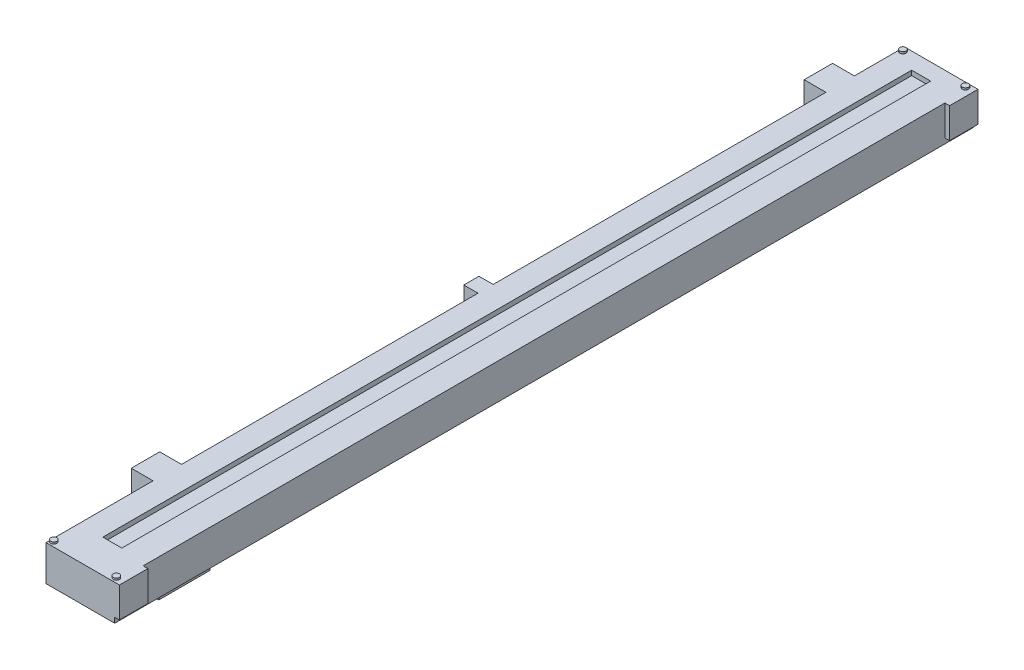
SolidWorks part; units mm, degrees
material "Delrin 2700 NC010, Low Viscosity Acetal Copolymer (SS)"
ref_plane "Front Plane" through (0, 0, 0) normal (0, 0, 1) x (1, 0, 0)
ref_plane "Top Plane" through (0, 0, 0) normal (0, 1, 0) x (1, 0, 0)
ref_plane "Right Plane" through (0, 0, 0) normal (1, 0, 0) x (0, 0, -1)
sketch "Sketch1" plane through (0, 0, 0) normal (0, 1, 0) x (1, 0, 0)
  line L0 (-9.2075, 115.0938) -> (9.2075, -115.0938) construction
  line L1 (-9.2075, 115.0938) -> (9.2075, 115.0938)
  line L2 (-9.2075, 115.0938) -> (-9.2075, -115.0938)
  line L3 (-9.2075, -115.0938) -> (9.2075, -115.0938)
  line L4 (9.2075, 115.0938) -> (9.2075, -115.0938)
  dimension "D1" = 18.415
  dimension "D2" = 230.1875
extrude "Boss-Extrude1" add sketch "Sketch1" along normal blind 9.525
sketch "Sketch2" plane through (0, 9.525, 0) normal (0, 1, 0) x (1, 0, 0)
  line L0 (-2.8575, 110.6487) -> (2.2225, -106.2038) construction
  line L1 (-2.8575, 110.6487) -> (2.2225, 110.6487)
  line L2 (-2.8575, 110.6487) -> (-2.8575, -106.2038)
  line L3 (-2.8575, -106.2038) -> (2.2225, -106.2038)
  line L4 (2.2225, 110.6487) -> (2.2225, -106.2038)
  line L5 (9.2075, 115.0938) -> (-9.2075, 115.0938) construction
  line L6 (-9.2075, -115.0938) -> (9.2075, -115.0938) construction
  line L8 (-9.2075, 115.0938) -> (-9.2075, -115.0938) construction
  dimension "D1" = 5.08
  dimension "D2" = 4.445
  dimension "D3" = 8.89
  dimension "D4" = 6.35
extrude "Cut-Extrude1" cut sketch "Sketch2" against normal blind 1.27
sketch "Sketch3" plane through (0, 9.525, 0) normal (0, 1, 0) x (1, 0, 0)
  line L0 (-9.2075, 115.0938) -> (-9.2075, -115.0938) construction
  line L1 (-9.2075, 101.6317) -> (-15.0495, 101.6317)
  line L2 (-9.2075, 101.6317) -> (-9.2075, 94.0117)
  line L3 (-9.2075, 94.0117) -> (-15.0495, 94.0117)
  line L4 (-15.0495, 101.6317) -> (-15.0495, 94.0117)
  line L5 (-9.2075, -115.0938) -> (9.2075, -115.0938) construction
  line L6 (-9.2075, 4.7942) -> (-13.0175, 4.7942)
  line L7 (-9.2075, 4.7942) -> (-9.2075, 0.7302)
  line L8 (-9.2075, 0.7302) -> (-13.0175, 0.7302)
  line L9 (-13.0175, 4.7942) -> (-13.0175, 0.7302)
  line L10 (-9.2075, -78.7718) -> (-15.0495, -78.7718)
  line L11 (-9.2075, -78.7718) -> (-9.2075, -86.3918)
  line L12 (-9.2075, -86.3918) -> (-15.0495, -86.3918)
  line L13 (-15.0495, -78.7718) -> (-15.0495, -86.3918)
  line L14 (9.2075, 115.0938) -> (-9.2075, 115.0938) construction
  line L15 (9.2075, -115.0938) -> (9.2075, 115.0938) construction
  line L16 (9.2075, 115.0938) -> (10.4775, 115.0938)
  line L17 (9.2075, 115.0938) -> (9.2075, 107.4737)
  line L18 (9.2075, 107.4737) -> (10.4775, 107.4737)
  line L19 (10.4775, 115.0938) -> (10.4775, 107.4737)
  line L20 (9.2075, -115.0938) -> (10.4775, -115.0938)
  line L21 (9.2075, -115.0938) -> (9.2075, -107.4738)
  line L22 (9.2075, -107.4738) -> (10.4775, -107.4738)
  line L23 (10.4775, -115.0938) -> (10.4775, -107.4738)
  dimension "D1" = 7.62
  dimension "D2" = 5.842
  dimension "D3" = 28.702
  dimension "D4" = 13.462
  dimension "D5" = 115.824
  dimension "D6" = 4.064
  dimension "D7" = 3.81
  dimension "D8" = 7.62
  dimension "D9" = 1.27
extrude "Boss-Extrude2" add sketch "Sketch3" against normal blind 8.128
sketch "Sketch4" plane through (0, 9.525, 0) normal (0, 1, 0) x (1, 0, 0)
  line L1 (8.382, 113.8237) -> (-8.382, 113.8238) construction
  line L2 (8.382, 113.8237) -> (8.382, -113.8238) construction
  line L3 (8.382, -113.8238) -> (-8.382, -113.8238) construction
  line L4 (-8.382, 113.8238) -> (-8.382, -113.8238) construction
  line L6 (9.2075, -107.4738) -> (9.2075, 107.4737) construction
  line L7 (-9.2075, 115.0938) -> (-9.2075, 101.6317) construction
  line L8 (10.4775, 115.0938) -> (-9.2075, 115.0938) construction
  line L9 (-9.2075, -115.0938) -> (10.4775, -115.0938) construction
  circle A0 centre (-8.382, 113.8238) radius 0.8255
  circle A1 centre (8.382, 113.8237) radius 0.8255
  circle A2 centre (8.382, -113.8238) radius 0.8255
  circle A3 centre (-8.382, -113.8238) radius 0.8255
  dimension "D1" = 1.651
  dimension "D2" = 1.27
  dimension "D3" = 1.27
extrude "Boss-Extrude3" add sketch "Sketch4" along normal blind 0.508
sketch "Sketch5" plane through (0, 0, 0) normal (0, -1, 0) x (1, 0, 0)
  line L0 (-9.2075, 115.0938) -> (9.2075, 115.0938) construction
  line L1 (6.9215, 100.9714) -> (1.8415, 100.9714)
  line L2 (6.9215, 100.9714) -> (6.9215, 87.2554)
  line L3 (6.9215, 87.2554) -> (1.8415, 87.2554)
  line L4 (1.8415, 100.9714) -> (1.8415, 87.2554)
  line L5 (9.2075, 115.0938) -> (9.2075, -115.0938) construction
  dimension "D1" = 5.08
  dimension "D2" = 13.716
  dimension "D3" = 14.1224
  dimension "D4" = 2.286
extrude "Boss-Extrude4" add sketch "Sketch5" along normal blind 2.794
